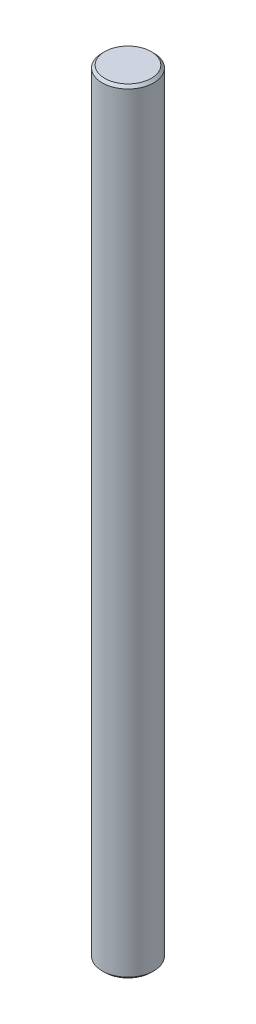
SolidWorks part; units mm, degrees
ref_plane "Front Plane" through (0, 0, 0) normal (0, 0, 1) x (1, 0, 0)
ref_plane "Top Plane" through (0, 0, 0) normal (0, 1, 0) x (1, 0, 0)
ref_plane "Right Plane" through (0, 0, 0) normal (1, 0, 0) x (0, 0, -1)
sketch "Sketch1" plane through (0, 0, 0) normal (0, 1, 0) x (1, 0, 0)
  circle A0 centre (0, 0) radius 10
  dimension "D1" = 20
extrude "Boss-Extrude1" add sketch "Sketch1" along normal blind 300
chamfer "Chamfer1" distance 1 angle 45 2 edges at (0, 300, 10) (0, 0, 10)
